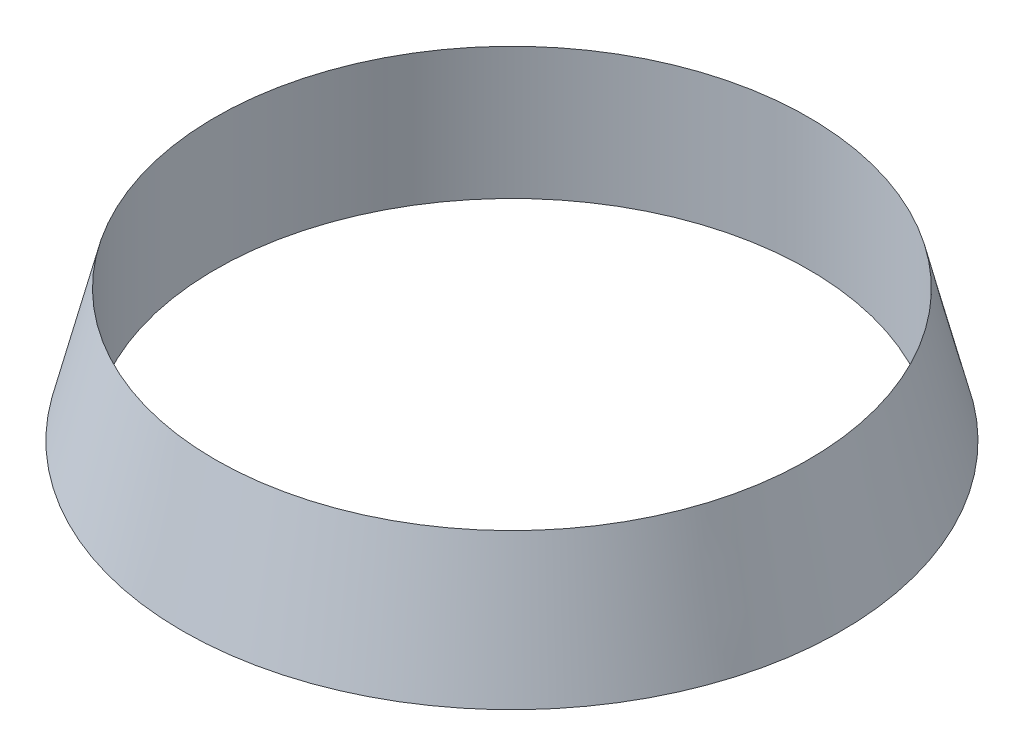
SolidWorks part; units mm, degrees
ref_plane "Front Plane" through (0, 0, 0) normal (0, 0, 1) x (1, 0, 0)
ref_plane "Top Plane" through (0, 0, 0) normal (0, 1, 0) x (1, 0, 0)
ref_plane "Right Plane" through (0, 0, 0) normal (1, 0, 0) x (0, 0, -1)
sketch "Sketch1" plane through (0, 0, 0) normal (0, 1, 0) x (1, 0, 0)
  circle A0 centre (0, 0) radius 50
  dimension "D1" = 100
ref_plane "Plane1" through (0, 20, 0) normal (0, 1, 0) x (1, 0, 0)
sketch "Sketch2" plane through (0, 20, 0) normal (0, 1, 0) x (1, 0, 0)
  circle A0 centre (0, 0) radius 45
  dimension "D1" = 90
loft "Loft1" add profiles "Sketch1", "Sketch2"
sketch "Sketch3" plane through (0, 20, 0) normal (0, 1, 0) x (1, 0, 0)
  circle A1 centre (0, 0) radius 45
  circle A2 centre (0, 0) radius 45
  dimension "D1" = 0
extrude "Cut-Extrude1" cut sketch "Sketch3" against normal through all
